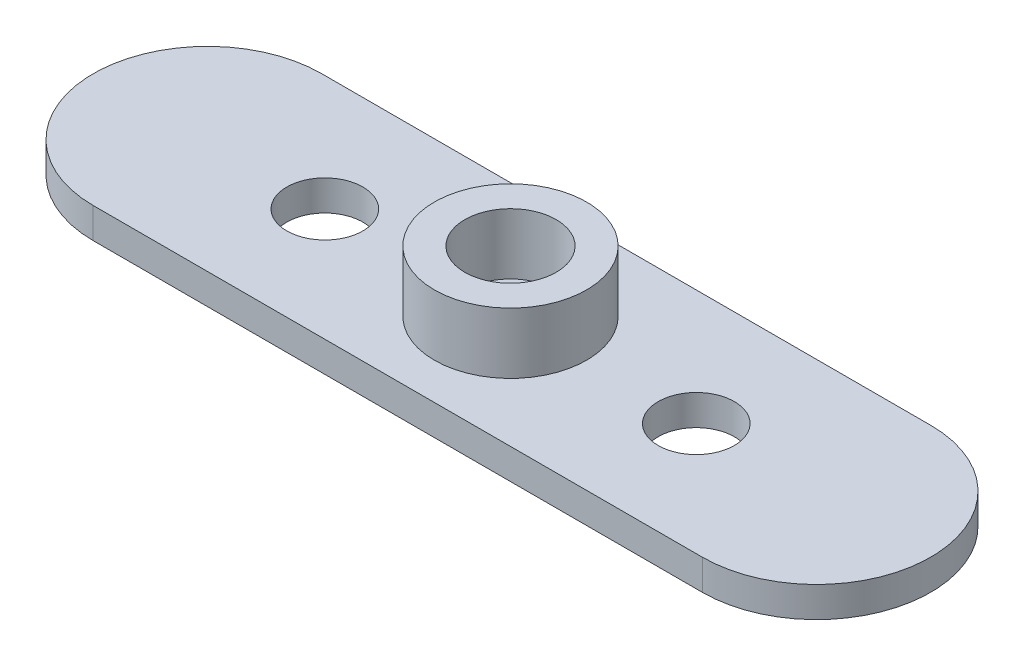
SolidWorks part; units mm, degrees
ref_plane "Front Plane" through (0, 0, 0) normal (0, 0, 1) x (1, 0, 0)
ref_plane "Top Plane" through (0, 0, 0) normal (0, 1, 0) x (1, 0, 0)
ref_plane "Right Plane" through (0, 0, 0) normal (1, 0, 0) x (0, 0, -1)
sketch "Sketch1" plane through (0, 0, 0) normal (0, 1, 0) x (1, 0, 0)
  line L0 (-20, 0.0986) -> (20, 0.0986) construction
  line L5 (-27.5, 0.0986) -> (27.5, 0.0986) construction
  line L6 (0, 7.5986) -> (0, -7.4014) construction
  line L7 (-20, 7.5986) -> (20, 7.5986)
  line L8 (-20, -7.4014) -> (20, -7.4014)
  arc A0 (-20, 7.5986) -> (-20, -7.4014) centre (-20, 0.0986) ccw
  arc A1 (20, -7.4014) -> (20, 7.5986) centre (20, 0.0986) ccw
  point P0 (0, 0)
  point P8 (0, 0.0986)
  dimension "D2" = 55
extrude "Boss-Extrude1" add sketch "Sketch1" along normal blind 2
sketch "Sketch2" plane through (0, 2, 0) normal (0, 1, 0) x (1, 0, 0)
  circle A0 centre (0, 0) radius 5
  dimension "D1" = 10
extrude "Boss-Extrude3" add sketch "Sketch2" along normal blind 4
sketch "Sketch5" plane through (0, 6, 0) normal (0, 1, 0) x (1, 0, 0)
  circle A0 centre (0, 0) radius 3
extrude "Cut-Extrude1" cut sketch "Sketch5" against normal up to surface (4 mm away) contours A0 up to face at (0, 2, 5)
sketch "Sketch6" plane through (0, 2, 0) normal (0, 1, 0) x (1, 0, 0)
  circle A0 centre (0, 0) radius 1.5
extrude "Cut-Extrude2" cut sketch "Sketch6" against normal blind 2
sketch "Sketch7" plane through (0, 2, 0) normal (0, 1, 0) x (1, 0, 0)
  circle A0 centre (12.2, 0) radius 2.5
  dimension "D1" = 5
  dimension "D2" = 12.2
sketch "Sketch8" plane through (0, 2, 0) normal (0, 1, 0) x (1, 0, 0)
  circle A0 centre (-12.2, 0.009) radius 2.5
  dimension "D1" = 5
  dimension "D2" = 12.2
extrude "Cut-Extrude3" cut sketch "Sketch8" against normal through all
extrude "Cut-Extrude4" cut sketch "Sketch7" against normal through all contours A0
